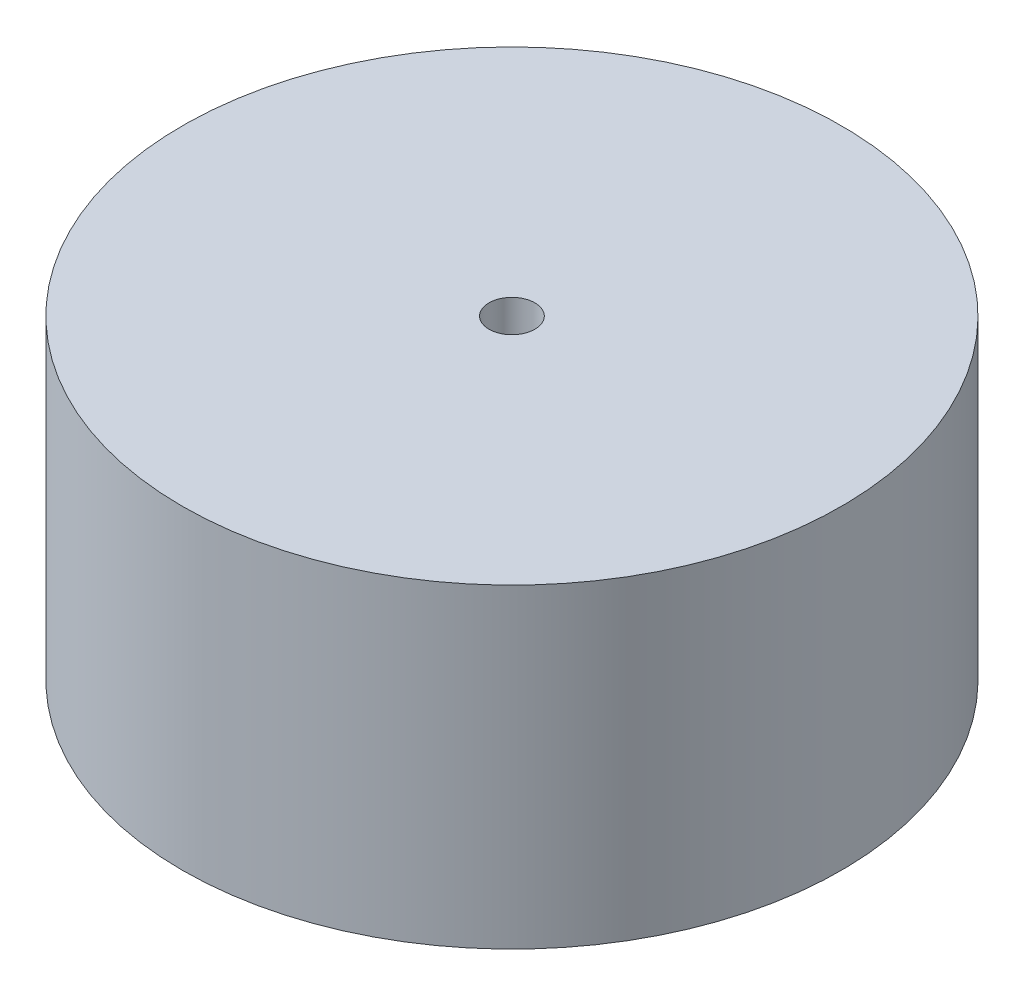
SolidWorks part; units mm, degrees
ref_plane "前视基准面" through (0, 0, 0) normal (0, 0, 1) x (1, 0, 0)
ref_plane "上视基准面" through (0, 0, 0) normal (0, 1, 0) x (1, 0, 0)
ref_plane "右视基准面" through (0, 0, 0) normal (1, 0, 0) x (0, 0, -1)
other "Configuration Table"
sketch "草图1" plane through (0, 0, 0) normal (0, 1, 0) x (1, 0, 0)
  circle A0 centre (0, 0) radius 23
  dimension "D1" = 46
extrude "凸台-拉伸1" add sketch "草图1" along normal blind 22
sketch "草图2" plane through (0, 22, 0) normal (0, 1, 0) x (1, 0, 0)
  circle A0 centre (0, 0) radius 1.6
  dimension "D1" = 3.2
extrude "切除-拉伸1" cut sketch "草图2" against normal through all both and the other way through all
